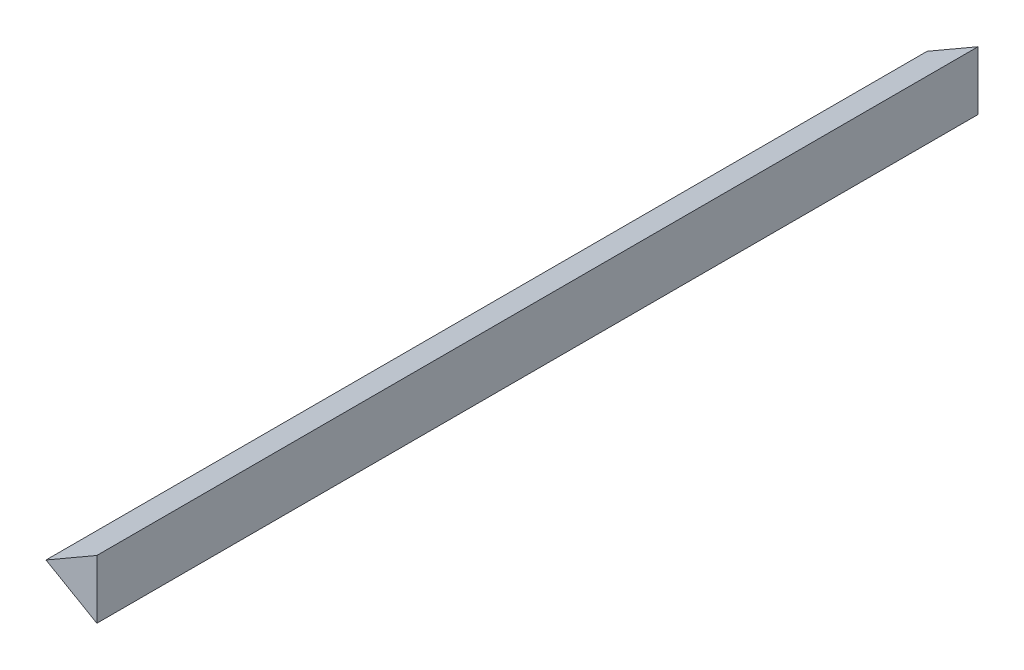
SolidWorks part; units mm, degrees
ref_plane "Front Plane"
ref_plane "Top Plane" through (0, 0, 0) normal (0, 1, 0) x (1, 0, 0)
ref_plane "Right Plane" through (0, 0, 0) normal (1, 0, 0) x (0, 0, -1)
sketch "Sketch1" plane through (0, 0, 0) normal (0, 0, 1) x (1, 0, 0)
  line L0 (120, 140) -> (154.641, 160)
  line L1 (120, 140) -> (154.641, 120)
  line L2 (154.641, 120) -> (154.641, 160)
  dimension "D1" = 120
  dimension "D2" = 40
  dimension "D3" = 40
  dimension "D4" = 40
  dimension "D5" = 120
  dimension "D6" = 140
extrude "Boss-Extrude1" add sketch "Sketch1" against normal blind 600
